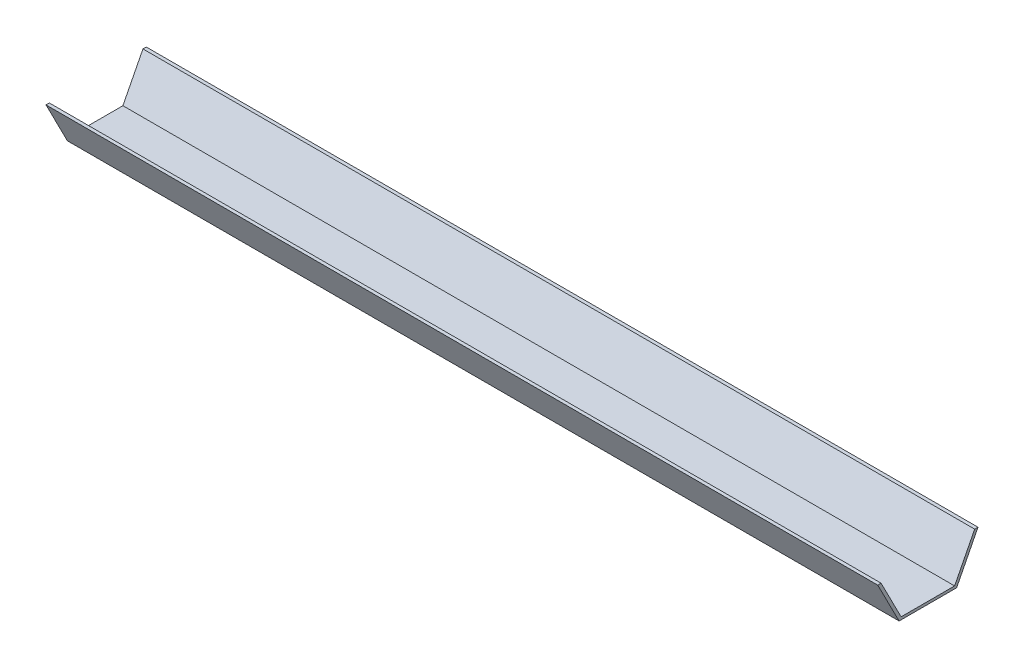
SolidWorks part; units mm, degrees
ref_plane "Front Plane" through (0, 0, 0) normal (0, 0, 1) x (1, 0, 0)
ref_plane "Top Plane" through (0, 0, 0) normal (0, 1, 0) x (1, 0, 0)
ref_plane "Right Plane" through (0, 0, 0) normal (1, 0, 0) x (0, 0, -1)
sketch "Sketch1" plane through (0, 0, 0) normal (1, 0, 0) x (0, 0, -1)
  line L0 (0, 0) -> (-22.9152, 0)
  line L1 (0, 0) -> (9.6372, 18.8461)
  line L2 (-23.5224, 1.1873) -> (0.6506, 1.1873)
  line L3 (-22.9152, 0) -> (-32.5524, 18.8461)
  line L4 (9.6372, 18.8461) -> (11.1445, 18.8461)
  line L5 (11.1445, 18.8461) -> (1.5073, 0)
  line L6 (1.5073, 0) -> (0.2163, 0)
  line L7 (-32.5524, 18.8461) -> (-34.0624, 18.8461)
  line L8 (-34.0624, 18.8461) -> (-24.4252, 0)
  line L9 (-24.4252, 0) -> (-22.9152, 0)
  line L10 (0.2163, 0) -> (0, 0)
  dimension "D1" = 1.5073
  dimension "D2" = 1.51
extrude "Boss-Extrude1" add sketch "Sketch1" along normal blind 375
